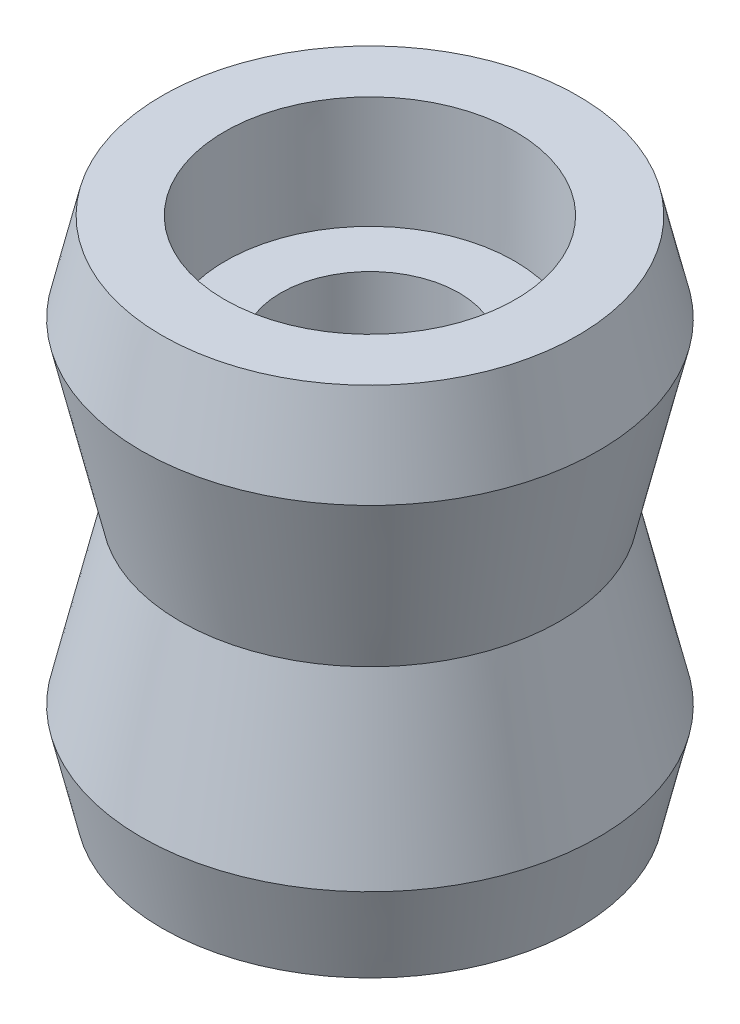
SolidWorks part; units mm, degrees
material "Maple"
ref_plane "Wasteboard" through (0, 0, 0) normal (0, 0, 1) x (1, 0, 0)
ref_plane "Left-Right" through (0, 0, 0) normal (0, 1, 0) x (1, 0, 0)
ref_plane "Front-Back" through (0, 0, 0) normal (1, 0, 0) x (0, 0, -1)
sketch "Sketch1" plane through (0, 0, 0) normal (0, 0, 1) x (1, 0, 0)
  line L0 (0, 42.3235) -> (0, -39.784) construction
  line L1 (0, -55) -> (0, 55) construction
  line L2 (0, 3.1923) -> (41.2814, 3.1923) construction
  line L3 (41.2814, 3.1923) -> (41.2814, 18.1923) construction
  line L4 (31.7163, 3.1923) -> (31.7163, 10.1923) construction
  line L5 (0, 30.7268) -> (2.5, 30.7268) construction
  line L6 (0, 37.5678) -> (4, 37.5678) construction
  line L7 (0, 43.5419) -> (6.5, 43.5419) construction
  line L8 (4, -3.3135) -> (4, 9.6982)
  line L9 (4, 9.6982) -> (6.48, 9.6982)
  line L11 (6.52, 14.6982) -> (9.3156, 14.6982)
  line L12 (9.3156, 14.6982) -> (10.25, 10.6923)
  line L13 (10.25, 10.6923) -> (8.5, 3.1923)
  line L19 (29.4361, 3.1923) -> (29.4361, 14.6923) construction
  line L20 (29.4361, 14.6923) -> (-15.0373, 14.6923) construction
  line L21 (6.52, 14.6982) -> (6.48, 9.6982)
  line L22 (10.25, 10.6923) -> (7.4676, 10.6923) construction
  line L25 (6.52, -8.3135) -> (6.48, -3.3135)
  line L26 (10.25, -4.3077) -> (8.5, 3.1923)
  line L27 (9.3156, -8.3135) -> (10.25, -4.3077)
  line L28 (6.52, -8.3135) -> (9.3156, -8.3135)
  line L29 (4, -3.3135) -> (6.48, -3.3135)
  point P25 (4, 3.1923)
  dimension "D1" = 15
  dimension "D2" = 7
  dimension "D3" = 4
  dimension "D4" = 2.5
  dimension "D5" = 6.5
  dimension "D6" = 6.25
  dimension "D7" = 7.5
  dimension "D8" = 76.866
  dimension "D9" = 2.52
  dimension "D10" = 82.1075
  dimension "D11" = 2.48
  dimension "D12" = 76.87
  dimension "D13" = 11.5
  dimension "D14" = 4.5
  dimension "D15" = 5
revolve "Revolve1" add sketch "Sketch1" angle 360 about L0
sketch "Sketch2" plane through (0, -3.3135, 0) normal (0, -1, 0) x (1, 0, 0)
  circle A3 centre (0, 0) radius 4 construction
  circle A4 centre (0, 0) radius 4
extrude "Boss-Extrude1" add sketch "Sketch2" against normal blind 0.2
